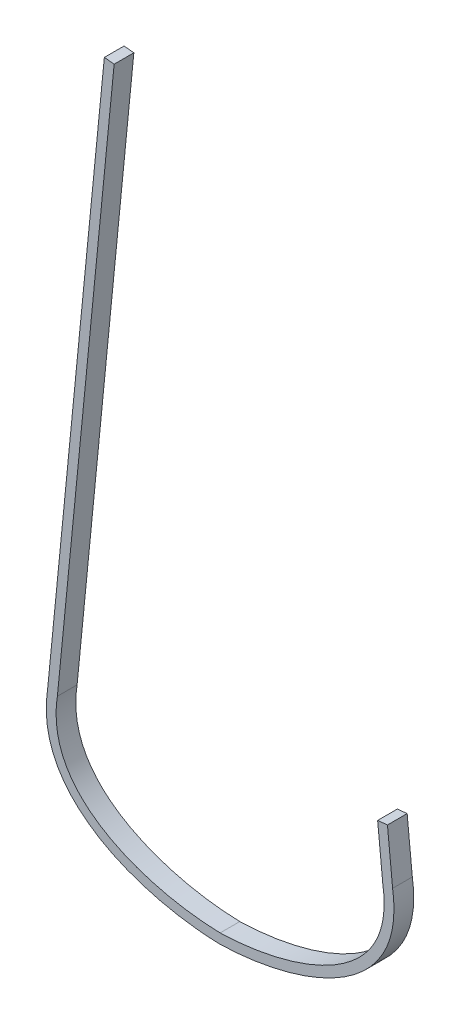
SolidWorks part; units mm, degrees
ref_plane "Front Plane" through (0, 0, 0) normal (0, 0, 1) x (1, 0, 0)
ref_plane "Top Plane" through (0, 0, 0) normal (0, 1, 0) x (1, 0, 0)
ref_plane "Right Plane" through (0, 0, 0) normal (1, 0, 0) x (0, 0, -1)
sketch "Sketch1" plane through (0, 0, 0) normal (0, 0, 1) x (1, 0, 0)
  line L0 (157.2341, 128.9805) -> (152.2242, 179.7953)
  line L1 (-157.2341, 128.9805) -> (-102.3813, 685.3442)
  line L2 (-111.8604, 686.2788) -> (-102.3813, 685.3442)
  line L3 (152.2242, 179.7953) -> (161.7032, 180.7299)
  line L4 (166.6875, 130.175) -> (106.8761, 736.8337) construction
  line L5 (157.2341, 128.9805) -> (97.8226, 731.5828) construction
  line L6 (-166.6875, 130.175) -> (-111.8604, 686.2788)
  line L7 (166.6875, 130.175) -> (161.7032, 180.7299)
  line L8 (106.8761, 736.8337) -> (0, 812.8) construction
  line L9 (97.8226, 731.5828) -> (0, 801.114) construction
  line L10 (-106.8761, 736.8337) -> (0, 812.8) construction
  line L11 (-97.8226, 731.5828) -> (0, 801.114) construction
  line L12 (-157.2341, 128.9805) -> (-97.8226, 731.5828) construction
  line L13 (-166.6875, 130.175) -> (-106.8761, 736.8337) construction
  spline S0 degree 3 poles (0, 0) (-73.6666, 1.7407) (-181.1881, 36.2008) (-166.6875, 130.175) knots 0 0 0 0 1 1 1 1
  spline S2 degree 3 poles (0, 0) (73.6666, 1.7407) (181.1881, 36.2008) (166.6875, 130.175) knots 0 0 0 0 1 1 1 1
  spline S6 degree 1 poles (0, 9.5278) (157.2341, 128.9805) knots 0 0 1 1 construction
  spline S7 degree 1 poles (0, 9.5278) (-157.2341, 128.9805) knots 0 0 1 1 construction
  spline S10 degree 3 poles (157.2341, 128.9805) (157.2612, 128.8048) (157.3166, 128.4467) (157.4158, 127.7819) (157.5841, 126.6011) (157.8817, 124.2773) (158.2064, 121.0104) (158.4372, 117.1902) (158.5402, 112.2214) (158.2964, 106.2423) (157.4427, 99.4182) (156.0586, 92.9236) (153.5414, 84.674) (149.1923, 75.0755) (142.1891, 64.5645) (130.6439, 51.8036) (112.4361, 38.1575) (90.5159, 27.6265) (71.6896, 21.0509) (57.1652, 17.0231) (42.4775, 13.8759) (30.3032, 11.9623) (20.7255, 10.8404) (13.6522, 10.199) (7.88, 9.8272) (3.3405, 9.6248) (1.1176, 9.5552) (0, 9.5278) knots 0.001057 0.001057 0.001057 0.001057 0.00301 0.004963 0.008868 0.01668 0.032303 0.047925 0.063548 0.094794 0.126039 0.157285 0.188531 0.251022 0.313513 0.376004 0.500986 0.625969 0.68846 0.750951 0.813442 0.875933 0.907179 0.938424 0.96967 0.985293 1.000916 1.000916 1.000916 1.000916
  spline S11 degree 3 poles (0, 9.5278) (-1.1176, 9.5552) (-3.3405, 9.6248) (-7.88, 9.8272) (-13.6522, 10.199) (-20.7255, 10.8404) (-30.3032, 11.9623) (-42.4775, 13.8759) (-57.1652, 17.0231) (-71.6896, 21.0509) (-90.5159, 27.6265) (-112.4361, 38.1575) (-130.6439, 51.8036) (-142.1891, 64.5645) (-149.1923, 75.0755) (-153.5414, 84.674) (-156.0586, 92.9236) (-157.4427, 99.4182) (-158.2964, 106.2423) (-158.5402, 112.2214) (-158.4372, 117.1902) (-158.2064, 121.0104) (-157.8817, 124.2773) (-157.5841, 126.6011) (-157.4158, 127.7819) (-157.3166, 128.4467) (-157.2612, 128.8048) (-157.2341, 128.9805) knots 0.001057 0.001057 0.001057 0.001057 0.01668 0.032303 0.063548 0.094794 0.126039 0.188531 0.251022 0.313513 0.376004 0.500986 0.625969 0.68846 0.750951 0.813442 0.844688 0.875933 0.907179 0.938424 0.954047 0.96967 0.985293 0.993104 0.99701 0.998963 1.000916 1.000916 1.000916 1.000916
  dimension "D2" = 333.375
  dimension "D3" = 9.525
  dimension "D5" = 50.8
extrude "Boss-Extrude1" add sketch "Sketch1" along normal blind 19.05
